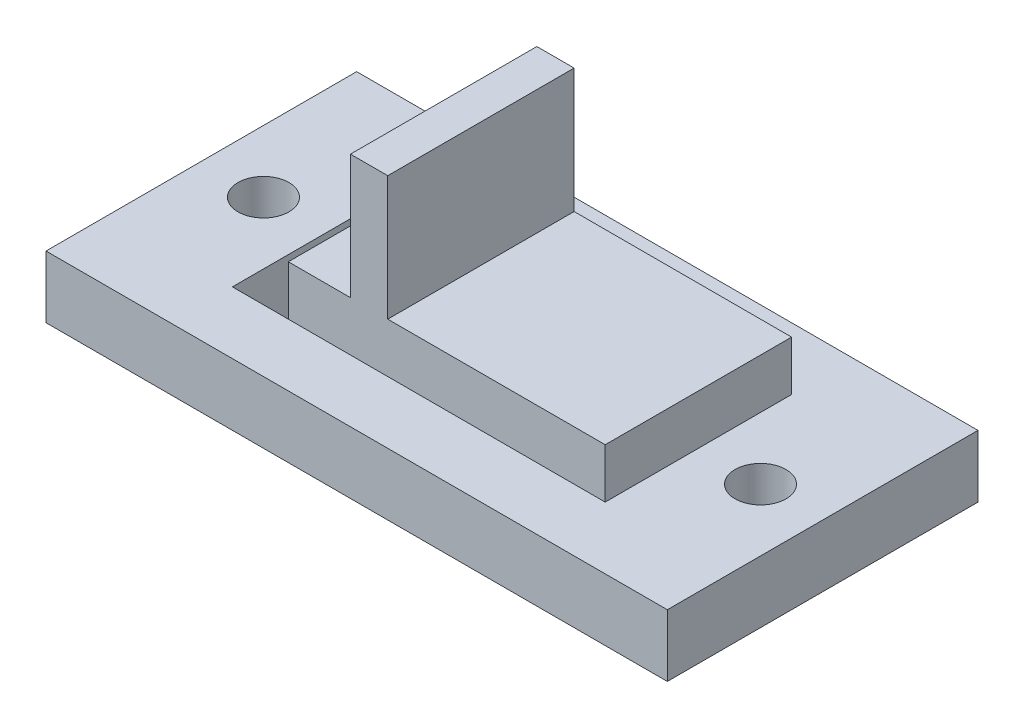
SolidWorks part; units mm, degrees
ref_plane "Front Plane" through (0, 0, 0) normal (0, 0, 1) x (1, 0, 0)
ref_plane "Top Plane" through (0, 0, 0) normal (0, 1, 0) x (1, 0, 0)
ref_plane "Right Plane" through (0, 0, 0) normal (1, 0, 0) x (0, 0, -1)
sketch "Sketch1" plane through (0, 0, 0) normal (0, 1, 0) x (1, 0, 0)
  line L1 (-12.7, -6.35) -> (12.7, -6.35)
  line L2 (-12.7, -6.35) -> (-12.7, 6.35)
  line L3 (-12.7, 6.35) -> (12.7, 6.35)
  line L4 (12.7, -6.35) -> (12.7, 6.35)
  line L5 (-12.7, -6.35) -> (12.7, 6.35) construction
  line L6 (-12.7, 6.35) -> (12.7, -6.35) construction
  point P0 (0, 0)
  dimension "D1" = 25.4
  dimension "D2" = 12.7
extrude "Boss-Extrude1" add sketch "Sketch1" along normal blind 2.54
sketch "Sketch2" plane through (0, 2.54, 0) normal (0, 1, 0) x (1, 0, 0)
  line L0 (12.7, 6.35) -> (-12.7, 6.35) construction
  line L1 (-7.62, -3.81) -> (7.62, -3.81)
  line L2 (-7.62, -3.81) -> (-7.62, 3.81)
  line L3 (-7.62, 3.81) -> (7.62, 3.81)
  line L4 (7.62, -3.81) -> (7.62, 3.81)
  line L5 (-7.62, -3.81) -> (7.62, 3.81) construction
  line L6 (-7.62, 3.81) -> (7.62, -3.81) construction
  line L7 (-12.7, 6.35) -> (-12.7, -6.35) construction
  point P0 (0, 0)
  dimension "D1" = 2.54
  dimension "D2" = 5.08
extrude "Boss-Extrude2" add sketch "Sketch2" along normal blind 2.032
sketch "Sketch3" plane through (0, 0, 0) normal (0, -1, 0) x (1, 0, 0)
  line L0 (-12.7, -6.35) -> (-12.7, 6.35) construction
  line L1 (12.7, 6.35) -> (12.7, -6.35) construction
  circle A0 centre (-10.16, 0) radius 1.0414
  circle A1 centre (10.16, 0) radius 1.0414
  point P6 (-12.7, 0)
  dimension "D1" = 2.54
  dimension "D2" = 2.54
extrude "Cut-Extrude1" cut sketch "Sketch3" against normal through all
sketch "Sketch4" plane through (0, 4.572, 0) normal (0, 1, 0) x (1, 0, 0)
  line L0 (7.62, 3.81) -> (-7.62, 3.81) construction
  line L1 (-7.62, -3.81) -> (-5.334, -3.81)
  line L2 (-7.62, -3.81) -> (-7.62, 3.81)
  line L3 (-7.62, 3.81) -> (-5.334, 3.81)
  line L4 (-5.334, -3.81) -> (-5.334, 3.81)
  dimension "D1" = 2.286
extrude "Cut-Extrude2" cut sketch "Sketch4" against normal up to surface (4.572 mm away) up to face at (-10.16, 0, -1.0414)
sketch "Sketch5" plane through (0, 4.572, 0) normal (0, 1, 0) x (1, 0, 0)
  line L0 (7.62, 3.81) -> (-5.334, 3.81) construction
  line L1 (-2.794, 3.81) -> (-1.27, 3.81)
  line L2 (-2.794, 3.81) -> (-2.794, -3.81)
  line L3 (-2.794, -3.81) -> (-1.27, -3.81)
  line L4 (-1.27, 3.81) -> (-1.27, -3.81)
  line L5 (-5.334, -3.81) -> (7.62, -3.81) construction
  line L6 (-5.334, -3.81) -> (-5.334, 3.81) construction
  dimension "D1" = 2.54
  dimension "D2" = 1.524
sketch "Sketch6" plane through (0, 4.572, 0) normal (0, 1, 0) x (1, 0, 0)
  line L0 (7.62, 3.81) -> (-5.334, 3.81) construction
  line L1 (1.016, 3.81) -> (3.048, 3.81)
  line L2 (1.016, 3.81) -> (1.016, -3.81)
  line L3 (1.016, -3.81) -> (3.048, -3.81)
  line L4 (3.048, 3.81) -> (3.048, -3.81)
  line L5 (-5.334, -3.81) -> (7.62, -3.81) construction
  line L6 (-1.27, 3.81) -> (-1.27, -3.81) construction
  line L8 (7.62, 3.81) -> (-5.334, 3.81) construction
  line L9 (5.334, 3.81) -> (7.62, 3.81)
  line L10 (5.334, 3.81) -> (5.334, -3.81)
  line L11 (5.334, -3.81) -> (7.62, -3.81)
  line L12 (7.62, 3.81) -> (7.62, -3.81)
  dimension "D1" = 2.032
  dimension "D2" = 2.286
  dimension "D3" = 2.286
extrude "Boss-Extrude3" add sketch "Sketch5" along normal blind 5.08
